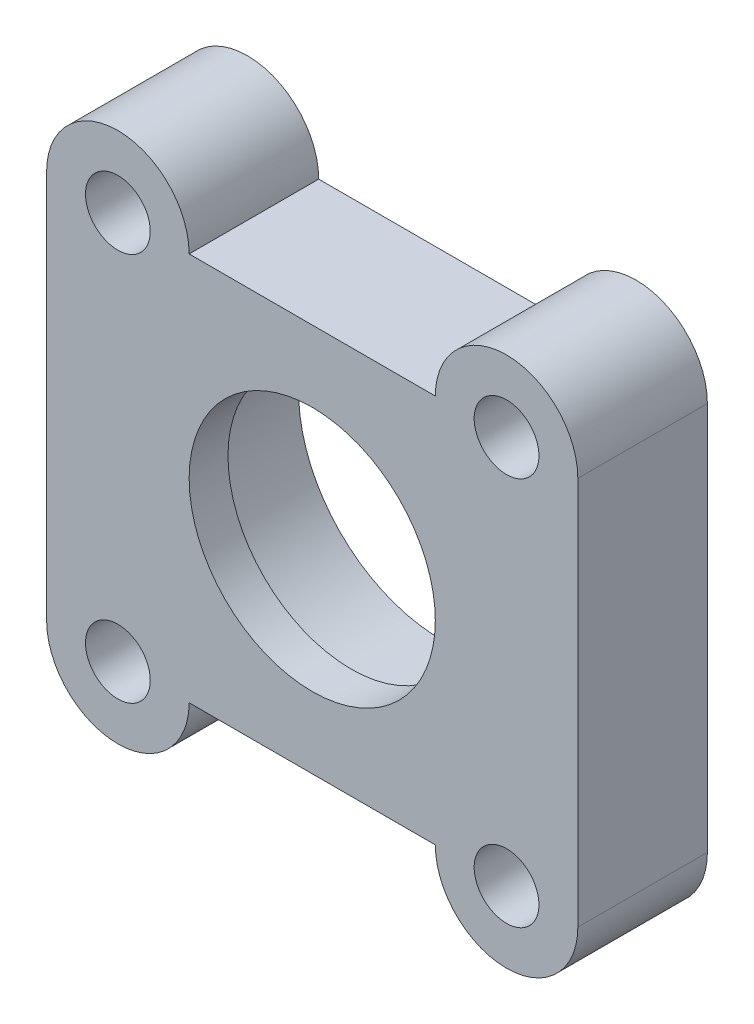
SolidWorks part; units mm, degrees
ref_plane "Alzado" through (0, 0, 0) normal (0, 0, 1) x (1, 0, 0)
ref_plane "Planta" through (0, 0, 0) normal (0, 1, 0) x (1, 0, 0)
ref_plane "Vista lateral" through (0, 0, 0) normal (1, 0, 0) x (0, 0, -1)
sketch "Croquis1" plane through (0, 0, 0) normal (0, 0, 1) x (1, 0, 0)
  line L0 (-37.3784, 26.1243) -> (-37.3784, 4.0243) construction
  line L1 (-57.8784, 30.0743) -> (-57.8784, 0.0743)
  line L2 (-37.3784, 26.1243) -> (-37.3784, 37.6855) construction
  line L3 (-37.3784, 4.0243) -> (-37.3784, -6.2432) construction
  line L4 (-21.0967, 15.0743) -> (-55.4356, 15.0743) construction
  line L5 (-27.8784, 30.0743) -> (-46.8784, 30.0743)
  line L6 (-27.8784, 0.0743) -> (-46.8784, 0.0743)
  line L16 (-16.8784, 30.0743) -> (-16.8784, 0.0743)
  circle A0 centre (-37.3784, 15.0743) radius 11.05
  circle A1 centre (-22.3784, 0.0743) radius 2.5
  circle A2 centre (-52.3784, 0.0743) radius 2.5
  circle A3 centre (-52.3784, 30.0743) radius 2.5
  circle A4 centre (-22.3784, 30.0743) radius 2.5
  arc A9 (-16.8784, 30.0743) -> (-27.8784, 30.0743) centre (-22.3784, 30.0743) ccw
  arc A10 (-57.8784, 30.0743) -> (-46.8784, 30.0743) centre (-52.3784, 30.0743) cw
  arc A11 (-57.8784, 0.0743) -> (-46.8784, 0.0743) centre (-52.3784, 0.0743) ccw
  arc A12 (-16.8784, 0.0743) -> (-27.8784, 0.0743) centre (-22.3784, 0.0743) cw
  dimension "D3" = 5.5
extrude "Saliente-Extruir1" add sketch "Croquis1" along normal blind 10
sketch "Croquis2" plane through (0, 0, 10) normal (0, 0, 1) x (1, 0, 0)
  line L0 (-37.3784, 26.1243) -> (-37.3784, 4.0243) construction
  circle A0 centre (-37.3784, 15.0743) radius 11.05 construction
  circle A1 centre (-37.3784, 15.0743) radius 13
  circle A2 centre (-37.3784, 15.0743) radius 9.5
extrude "Saliente-Extruir2" add sketch "Croquis2" against normal blind 3
